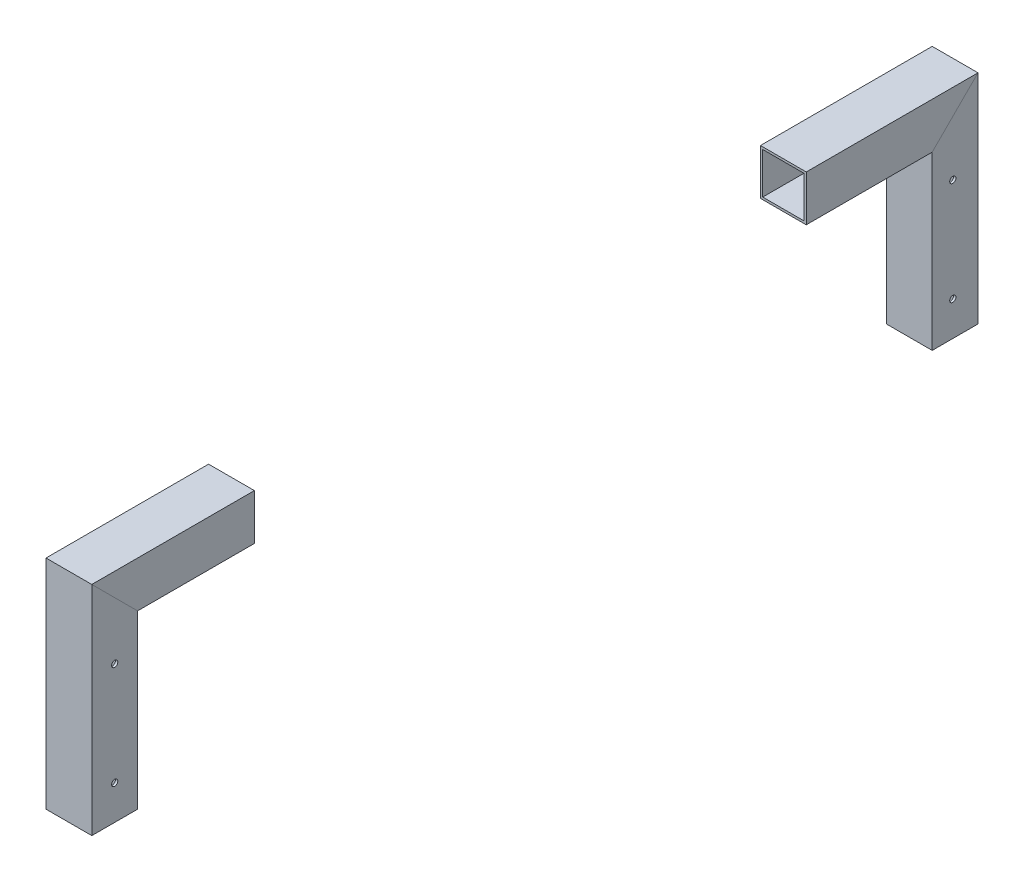
SolidWorks part; units mm, degrees
material "6063-O"
ref_plane "Front" through (0, 0, 0) normal (0, 0, 1) x (1, 0, 0)
ref_plane "Top" through (0, 0, 0) normal (0, 1, 0) x (1, 0, 0)
ref_plane "Right" through (0, 0, 0) normal (1, 0, 0) x (0, 0, -1)
sketch "草图1" plane through (0, 0, 0) normal (1, 0, 0) x (0, 0, -1)
  line L0 (0, 0) -> (0, 85)
  line L1 (0, 85) -> (367, 85)
  line L2 (367, 85) -> (367, 0)
  dimension "D1" = 367
  dimension "D2" = 85
other "铝管 20X20X1(1)"
ref_plane "基准面1" through (0, 0, 0) normal (0, 1, 0) x (0, 0, 1)
sketch "草图11" plane through (0, 0, 0) normal (0, 1, 0) x (0, 0, 1)
  line L1 (-10, -10) -> (10, -10)
  line L2 (-10, -10) -> (-10, 10)
  line L3 (-10, 10) -> (10, 10)
  line L4 (10, -10) -> (10, 10)
  line L5 (-10, -10) -> (10, 10) construction
  line L6 (-10, 10) -> (10, -10) construction
  line L7 (-9, -9) -> (9, -9)
  line L8 (-9, -9) -> (-9, 9)
  line L9 (-9, 9) -> (9, 9)
  line L10 (9, -9) -> (9, 9)
  line L11 (-9, -9) -> (9, 9) construction
  line L12 (-9, 9) -> (9, -9) construction
  point P0 (0, 0)
  point P6 (0, 0)
  point P11 (0, 0)
  dimension "D1" = 20
  dimension "D2" = 20
  dimension "D3" = 18
  dimension "D4" = 18
sketch "草图12" plane through (10, 0, 0) normal (1, 0, 0) x (0, 0, -1)
  line L0 (357, 75) -> (10, 75) construction
  line L1 (-10, 81) -> (314.2891, 81) construction
  line L2 (-10, 95) -> (-10, 0) construction
  line L3 (183.5, 95) -> (183.5, 75) construction
  line L4 (377, 95) -> (-10, 95) construction
  circle A0 centre (133.5, 81) radius 1.5
  circle A1 centre (233.5, 81) radius 1.5
  dimension "D1" = 6
  dimension "D2" = 3
  dimension "D3" = 3
  dimension "D4" = 100
extrude "切除-拉伸1" cut sketch "草图12" against normal up to surface (20 mm away) up to face at (-10, 85, -183.5)
sketch "草图13" plane through (0, 95, 0) normal (0, 1, 0) x (1, 0, 0)
  line L0 (0, 377) -> (0, -10) construction
  line L1 (10, 377) -> (-10, 377) construction
  line L2 (-10, -10) -> (10, -10) construction
  line L3 (-10, 377) -> (10, 377) construction
  line L4 (0, 352) -> (0, -35) construction
  line L5 (0, 327) -> (0, -60) construction
  line L6 (0, 302) -> (0, -85) construction
  line L7 (0, 277) -> (0, -110) construction
  line L8 (0, 252) -> (0, -135) construction
  line L9 (0, 227) -> (0, -160) construction
  line L10 (0, 202) -> (0, -185) construction
  line L11 (0, 177) -> (0, -210) construction
  line L12 (0, 152) -> (0, -235) construction
  line L13 (0, 127) -> (0, -260) construction
  line L14 (0, 102) -> (0, -285) construction
  circle A0 centre (0, 337) radius 6
  circle A1 centre (0, 312) radius 6
  circle A2 centre (0, 287) radius 6
  circle A3 centre (0, 262) radius 6
  circle A4 centre (0, 237) radius 6
  circle A5 centre (0, 212) radius 6
  circle A6 centre (0, 187) radius 6
  circle A7 centre (0, 162) radius 6
  circle A8 centre (0, 137) radius 6
  circle A9 centre (0, 112) radius 6
  circle A10 centre (0, 87) radius 6
  circle A11 centre (0, 62) radius 6
  dimension "D1" = 12
  dimension "D2" = 40
extrude "切除-拉伸2" [suppressed] cut sketch "草图13" against normal through all
sketch "草图14" plane through (10, 0, 0) normal (1, 0, 0) x (0, 0, -1)
  line L0 (357, 75) -> (10, 75) construction
  line L1 (61, 75) -> (302, 75)
  line L2 (61, 75) -> (61, 95)
  line L3 (61, 95) -> (302, 95)
  line L4 (302, 75) -> (302, 95)
  line L5 (377, 95) -> (-10, 95) construction
  line L6 (-10, 95) -> (-10, 0) construction
  line L7 (377, 0) -> (377, 95) construction
  dimension "D1" = 71
  dimension "D2" = 75
extrude "切除-拉伸3" cut sketch "草图14" against normal through all
sketch "草图15" plane through (10, 0, 0) normal (1, 0, 0) x (0, 0, -1)
  circle A0 centre (366, 60) radius 1.35
  circle A1 centre (366, 15) radius 1.35
  circle A2 centre (0, 60) radius 1.35
  circle A3 centre (0, 15) radius 1.35
  dimension "D1" = 2.7
  dimension "D2" = 2.7
  dimension "D3" = 2.7
  dimension "D4" = 2.7
extrude "切除-拉伸4" cut sketch "草图15" against normal blind 20
